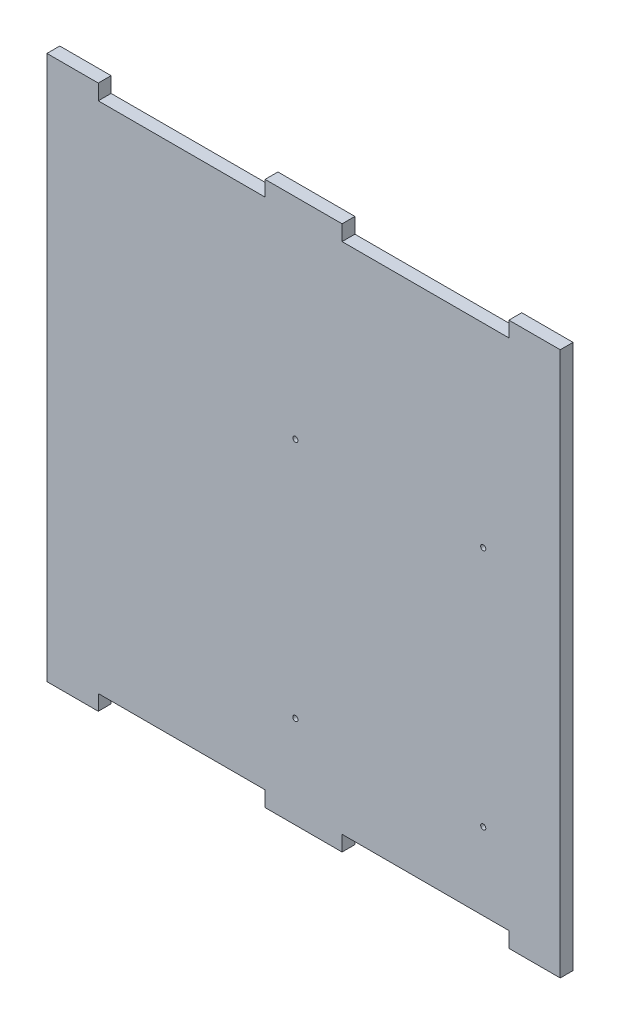
SolidWorks part; units mm, degrees
ref_plane "Plan de face" through (0, 0, 0) normal (0, 0, 1) x (1, 0, 0)
ref_plane "Plan de dessus" through (0, 0, 0) normal (0, 1, 0) x (1, 0, 0)
ref_plane "Plan de droite" through (0, 0, 0) normal (1, 0, 0) x (0, 0, -1)
sketch "Esquisse1" plane through (0, 0, 0) normal (0, 0, 1) x (1, 0, 0)
  line L0 (0, 0) -> (0, 212)
  line L1 (0, 212) -> (20, 212)
  line L2 (20, 212) -> (20, 206)
  line L3 (20, 206) -> (85, 206)
  line L4 (180, 206) -> (180, 212)
  line L5 (180, 212) -> (200, 212)
  line L6 (200, 212) -> (200, 0)
  line L7 (200, 0) -> (180, 0)
  line L8 (180, 0) -> (180, 6)
  line L9 (85, 212) -> (115, 212)
  line L10 (20, 6) -> (20, 0)
  line L11 (20, 0) -> (0, 0)
  line L12 (115, 212) -> (115, 206)
  line L13 (115, 206) -> (180, 206)
  line L14 (20, 6) -> (85, 6)
  line L15 (85, 6) -> (85, 0)
  line L16 (85, 0) -> (115, 0)
  line L17 (115, 0) -> (115, 6)
  line L18 (115, 6) -> (180, 6)
  line L19 (85, 206) -> (85, 212)
  circle A0 centre (170, 36) radius 1
  circle A1 centre (96.8, 36) radius 1
  circle A2 centre (96.8, 130.2) radius 1
  circle A3 centre (170, 130.2) radius 1
  point P23 (0, 0)
  point P31 (60.56, 36.6499)
  dimension "D5" = 2
  dimension "D17" = 30
  dimension "D1" = 20
  dimension "D2" = 20
  dimension "D3" = 200
  dimension "D4" = 212
  dimension "D6" = 6
  dimension "D7" = 6
  dimension "D8" = 20
  dimension "D9" = 30
  dimension "D10" = 30
  dimension "D11" = 6
  dimension "D12" = 6
  dimension "D13" = 65
  dimension "D14" = 65
  dimension "D15" = 2
  dimension "D16" = 2
  dimension "D18" = 30
  dimension "D19" = 94.2
  dimension "D20" = 73.2
extrude "Boss.-Extru.1" add sketch "Esquisse1" along normal blind 5
